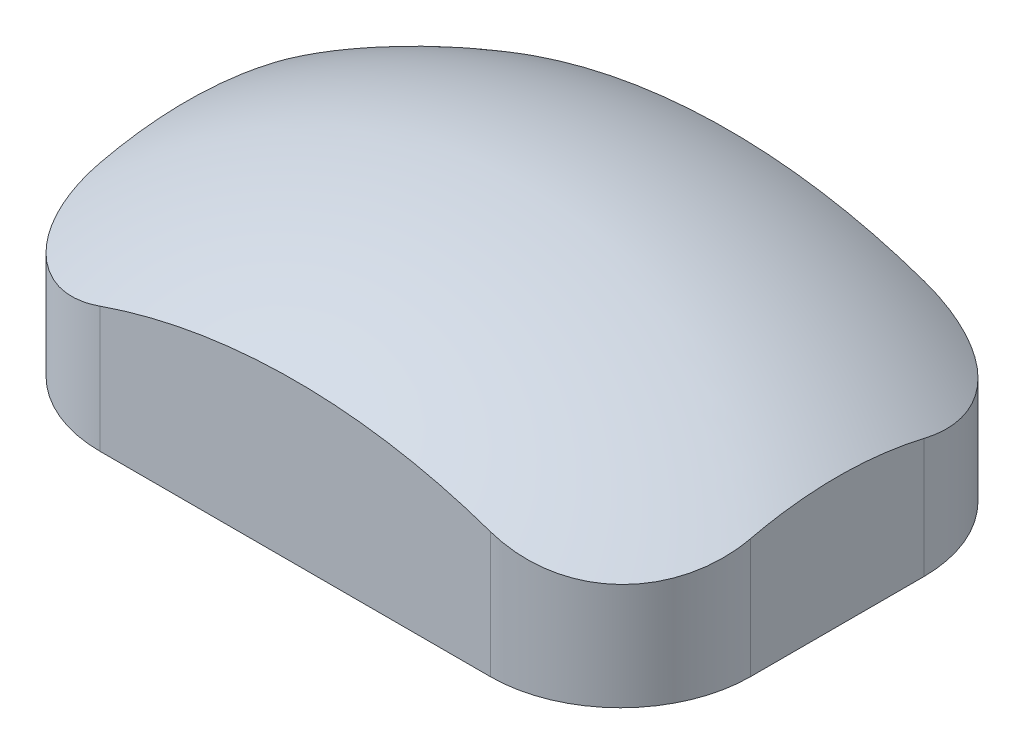
SolidWorks part; units mm, degrees
ref_plane "Plan de face" through (0, 0, 0) normal (0, 0, 1) x (1, 0, 0)
ref_plane "Plan de dessus" through (0, 0, 0) normal (0, 1, 0) x (1, 0, 0)
ref_plane "Plan de droite" through (0, 0, 0) normal (1, 0, 0) x (0, 0, -1)
sketch "Esquisse2" plane through (0, 0, 0) normal (0, 1, 0) x (1, 0, 0)
  line L0 (-75, 50) -> (75, -50) construction
  line L1 (-75, 50) -> (75, 50)
  line L2 (-75, 50) -> (-75, -50)
  line L3 (-75, -50) -> (75, -50)
  line L4 (75, 50) -> (75, -50)
  dimension "D1" = 100
  dimension "D2" = 150
extrude "Boss.-Extru.1" add sketch "Esquisse2" along normal blind 50
sketch "Esquisse3" plane through (0, 0, 0) normal (0, 0, 1) x (1, 0, 0)
  line L0 (-1050.4331, -100) -> (48949.5669, -100) construction
  line L1 (0, -44.1239) -> (0, 44.1239) construction
  line L2 (-75, 50) -> (75, 50) construction
  line L9 (-111.8034, 0) -> (111.8034, 0) construction
  arc A0 (111.8034, 0) -> (-111.8034, 0) centre (0, -100) ccw
  dimension "D1" = 150
sketch "Esquisse4" plane through (0, 0, 0) normal (1, 0, 0) x (0, 0, -1)
  line L0 (-86.6025, 0) -> (86.6025, 0) construction
  line L1 (-50, 50) -> (50, 50) construction
  line L2 (0, 27.5) -> (0, -27.5) construction
  line L3 (-86.6025, 0) -> (-86.6025, 100)
  line L4 (86.6025, 0) -> (86.6025, 100)
  line L5 (-86.6025, 100) -> (86.6025, 100)
  arc A0 (-86.6025, 0) -> (86.6025, 0) centre (0, -50) cw
  dimension "D1" = 100
  dimension "D2" = 100
sweep "Enlèvement de matière-Balayage1" cut profiles "Esquisse4" path "Esquisse3"
fillet "Congé1" radius 30 4 edges at (-75, 7.086, 50) (-75, 7.086, -50) (75, 7.086, -50) (75, 7.086, 50)
